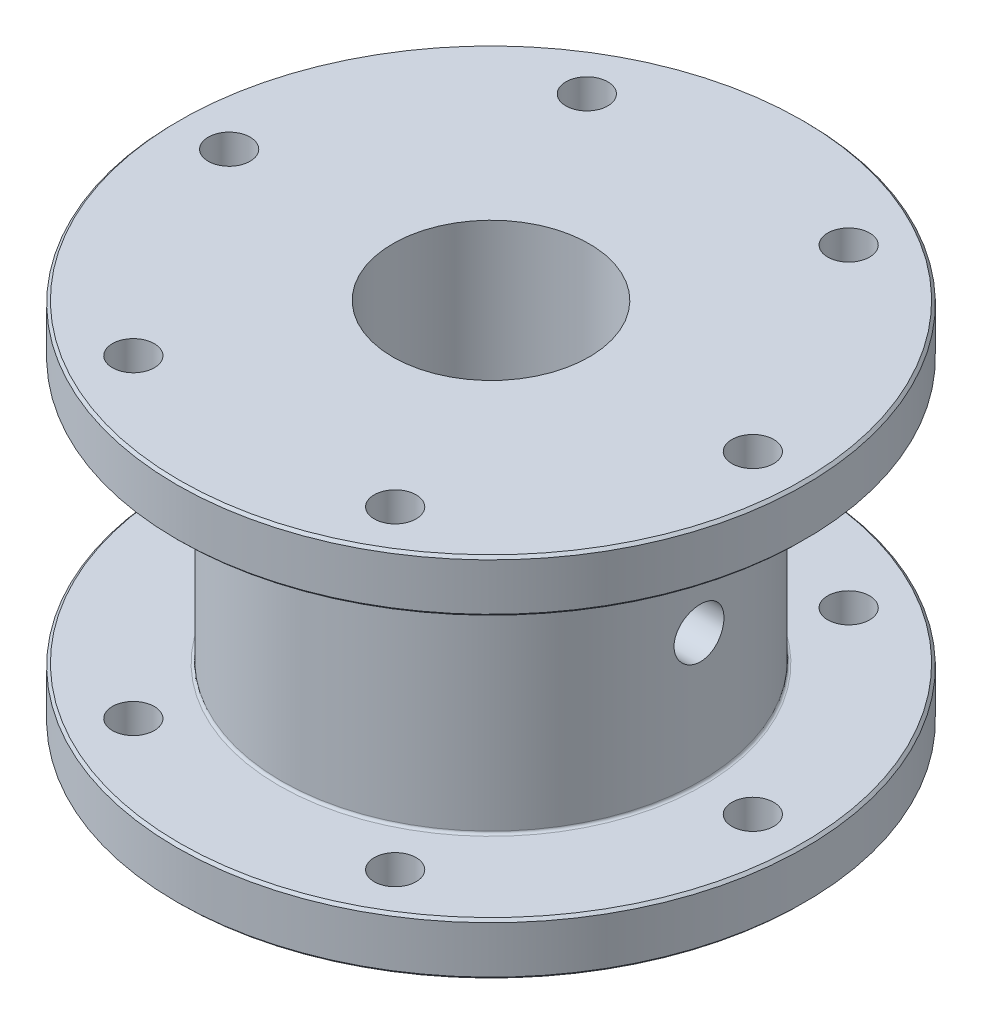
SolidWorks part; units mm, degrees
material "AISI 1020"
ref_plane "Alzado" through (0, 0, 0) normal (0, 0, 1) x (1, 0, 0)
ref_plane "Planta" through (0, 0, 0) normal (0, 1, 0) x (1, 0, 0)
ref_plane "Vista lateral" through (0, 0, 0) normal (1, 0, 0) x (0, 0, -1)
sketch "Croquis1" plane through (0, 0, 0) normal (0, 1, 0) x (1, 0, 0)
  line L0 (0, 0) -> (25, -43.3013) construction
  line L1 (50, 0) -> (25, 43.3013) construction
  line L2 (25, 43.3013) -> (-25, 43.3013) construction
  line L3 (-25, 43.3013) -> (-50, 0) construction
  line L4 (-50, 0) -> (-25, -43.3013) construction
  line L5 (-25, -43.3013) -> (25, -43.3013) construction
  line L6 (25, -43.3013) -> (50, 0) construction
  circle A0 centre (0, 0) radius 18.75
  circle A1 centre (0, 0) radius 60
  circle A2 centre (0, 0) radius 43.3013 construction
  circle A3 centre (25, -43.3013) radius 4
  circle A4 centre (-25, -43.3013) radius 4
  circle A5 centre (-50, 0) radius 4
  circle A6 centre (-25, 43.3013) radius 4
  circle A7 centre (25, 43.3013) radius 4
  circle A8 centre (50, 0) radius 4
  dimension "D1" = 37.5
  dimension "D5" = 8
  dimension "D6" = 120
  dimension "D2" = 50
  dimension "D4" = 50
  dimension "D3" = 6
extrude "Saliente-Extruir1" add sketch "Croquis1" along normal blind 10
sketch "Croquis2" plane through (0, 10, 0) normal (0, 1, 0) x (1, 0, 0)
  circle A0 centre (0, 0) radius 18.75
  circle A1 centre (0, 0) radius 40
  dimension "D1" = 37.5
  dimension "D2" = 80
extrude "Saliente-Extruir2" add sketch "Croquis2" along normal blind 50
chamfer "Chaflán2" distance 0.5 angle 45 2 edges at (0, 10, 60) (0, 0, 60)
fillet "Redondeo1" radius 0.5 1 edges at (0, 10, 40)
sketch "Croquis3" plane through (0, 0, 0) normal (1, 0, 0) x (0, 0, -1)
  line L0 (0, 60) -> (0, 10) construction
  line L2 (59.5, 10) -> (-59.5, 10) construction
  circle A0 centre (0, 35) radius 4.7625
  point P11 (-91.0846, 62.1052)
  dimension "D1" = 9.525
  dimension "D3" = 25
  dimension "D4" = 35
extrude "Cortar-Extruir1" cut sketch "Croquis3" against normal through all and the other way through all
ref_plane "Plano1" through (0, 35, 0) normal (0, 1, 0) x (1, 0, 0)
mirror "Simetría1" about plane through (0, 35, 0) normal (0, 1, 0) of "Saliente-Extruir1"
chamfer "Chaflán3" distance 0.5 angle 45 2 edges at (0, 70, 60) (0, 60, 60)
fillet "Redondeo3" radius 0.5 1 edges at (0, 60, 40)
